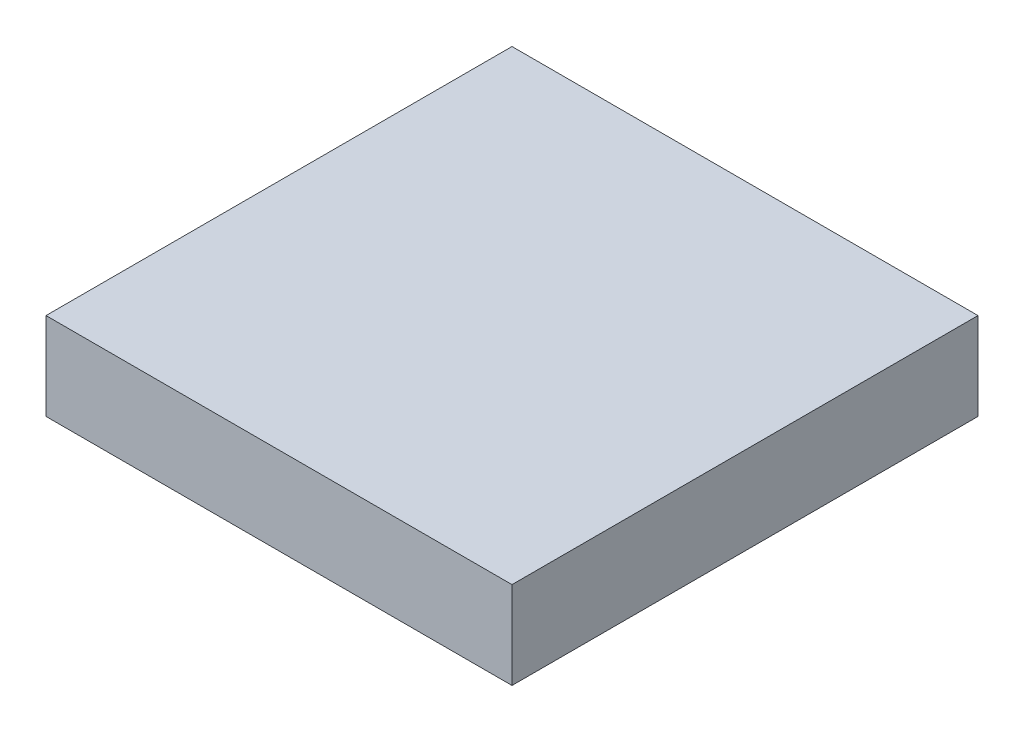
SolidWorks part; units mm, degrees
material "AISI 1020"
ref_plane "Front Plane" through (0, 0, 0) normal (0, 0, 1) x (1, 0, 0)
ref_plane "Top Plane" through (0, 0, 0) normal (0, 1, 0) x (1, 0, 0)
ref_plane "Right Plane" through (0, 0, 0) normal (1, 0, 0) x (0, 0, -1)
sketch "Sketch1" plane through (0, 0, 0) normal (0, 0, 1) x (1, 0, 0)
  line L1 (-101.6, 19.05) -> (101.6, 19.05)
  line L2 (-101.6, 19.05) -> (-101.6, -19.05)
  line L3 (-101.6, -19.05) -> (101.6, -19.05)
  line L4 (101.6, 19.05) -> (101.6, -19.05)
  line L5 (-101.6, 19.05) -> (101.6, -19.05) construction
  line L6 (-101.6, -19.05) -> (101.6, 19.05) construction
  point P1 (0, 0)
  dimension "D1" = 203.2
  dimension "D2" = 38.1
extrude "Boss-Extrude1" add sketch "Sketch1" along normal blind 203.2
